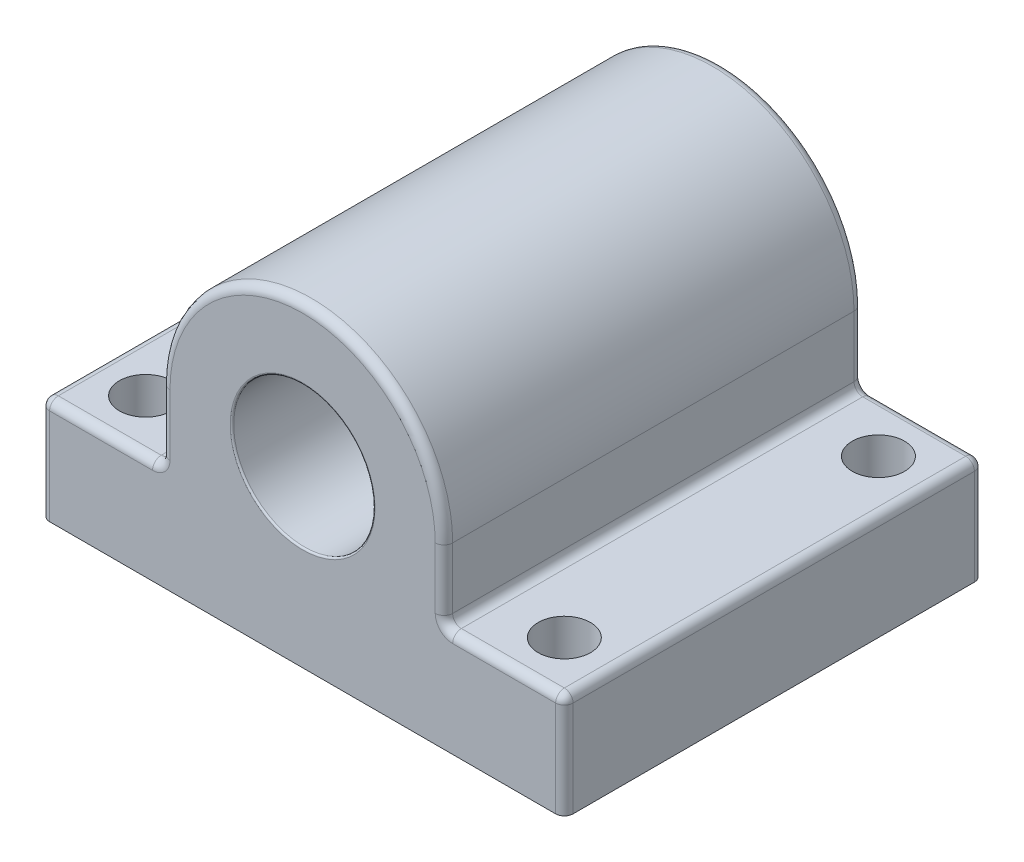
SolidWorks part; units mm, degrees
material "Aleación 2014"
ref_plane "Front Plane" through (0, 0, 0) normal (0, 0, 1) x (1, 0, 0)
ref_plane "Top Plane" through (0, 0, 0) normal (0, 1, 0) x (1, 0, 0)
ref_plane "Right Plane" through (0, 0, 0) normal (1, 0, 0) x (0, 0, -1)
sketch "Croquis1" plane through (0, 0, 0) normal (0, 0, 1) x (1, 0, 0)
  line L0 (15, 0) -> (-15, 0)
  line L1 (-15, 0) -> (-15, 10) construction
  line L3 (15, 10) -> (15, 0) construction
  line L4 (4.05, 10) -> (-4.05, 10) construction
  line L5 (-4.05, 10) -> (-15, 10) construction
  line L6 (4.05, 10) -> (15, 10) construction
  line L7 (0, 10) -> (0, 0) construction
  line L8 (-15, 0) -> (-15, 6)
  line L9 (-15, 6) -> (-8.1, 6)
  line L10 (-8.1, 6) -> (-8.1, 10)
  line L11 (8.1, 10) -> (8.1, 6)
  line L12 (8.1, 6) -> (15, 6)
  line L13 (15, 6) -> (15, 0)
  line L14 (8.1, 6) -> (-8.1, 6) construction
  circle A0 centre (0, 10) radius 4.05
  arc A1 (8.1, 10) -> (-8.1, 10) centre (0, 10) ccw
  point P4 (0, 0)
  point P13 (0, 10)
  dimension "D1" = 8.1
  dimension "D2" = 8.1
  dimension "D3" = 10
  dimension "D4" = 30
  dimension "D5" = 6
extrude "Saliente-Extruir1" add sketch "Croquis1" against normal mid plane 24 contours A0 L5 L1 L0 L3 L6 | L6 A1 L5 A0
sketch "Croquis2" plane through (0, 6, 0) normal (0, 1, 0) x (1, 0, 0)
  line L1 (12, -9) -> (-12, -9) construction
  line L2 (12, -9) -> (12, 9) construction
  line L3 (12, 9) -> (-12, 9) construction
  line L4 (-12, -9) -> (-12, 9) construction
  line L5 (12, -9) -> (-12, 9) construction
  line L6 (12, 9) -> (-12, -9) construction
  circle A0 centre (-12, 9) radius 1.5
  circle A1 centre (12, 9) radius 1.5
  circle A2 centre (-12, -9) radius 1.5
  circle A3 centre (12, -9) radius 1.5
  point P0 (0, 0)
  dimension "D3" = 3
  dimension "D1" = 24
  dimension "D2" = 18
extrude "Cortar-Extruir1" cut sketch "Croquis2" against normal up to next
fillet "Redondeo1" radius 0.5 18 edges at (11.55, 6, 12) (11.55, 6, -12) (8.1, 8, 12) (8.1, 8, -12) (0, 18.1, 12) (0, 18.1, -12) (-11.55, 6, -12) (-8.1, 8, 12) (-8.1, 8, -12) (-15, 3, -12) (15, 3, -12) (15, 3, 12) (-15, 3, 12) (15, 6, 0) (8.1, 6, 0) (-15, 6, 0) (-11.55, 6, 12) (-8.1, 6, 0)
fillet "Redondeo2" radius 0.1 2 edges at (4.05, 10, -12) (4.05, 10, 12)
